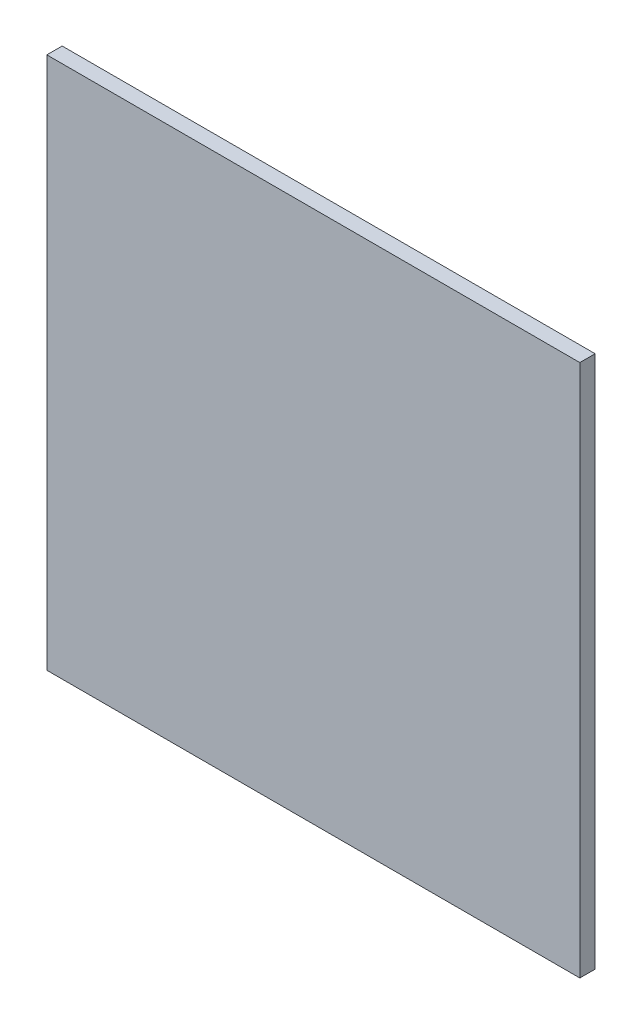
SolidWorks part; units mm, degrees
ref_plane "Front Plane" through (0, 0, 0) normal (0, 0, 1) x (1, 0, 0)
ref_plane "Top Plane" through (0, 0, 0) normal (0, 1, 0) x (1, 0, 0)
ref_plane "Right Plane" through (0, 0, 0) normal (1, 0, 0) x (0, 0, -1)
sketch "Sketch1" plane through (0, 0, 0) normal (0, 0, 1) x (1, 0, 0)
  line L1 (-90.9991, -374.4057) -> (69.0009, -374.4057)
  line L2 (-90.9991, -374.4057) -> (-90.9991, -214.4057)
  line L3 (-90.9991, -214.4057) -> (69.0009, -214.4057)
  line L4 (69.0009, -374.4057) -> (69.0009, -214.4057)
  dimension "D1" = 160
  dimension "D2" = 160
extrude "Boss-Extrude1" add sketch "Sketch1" along normal blind 4.6
